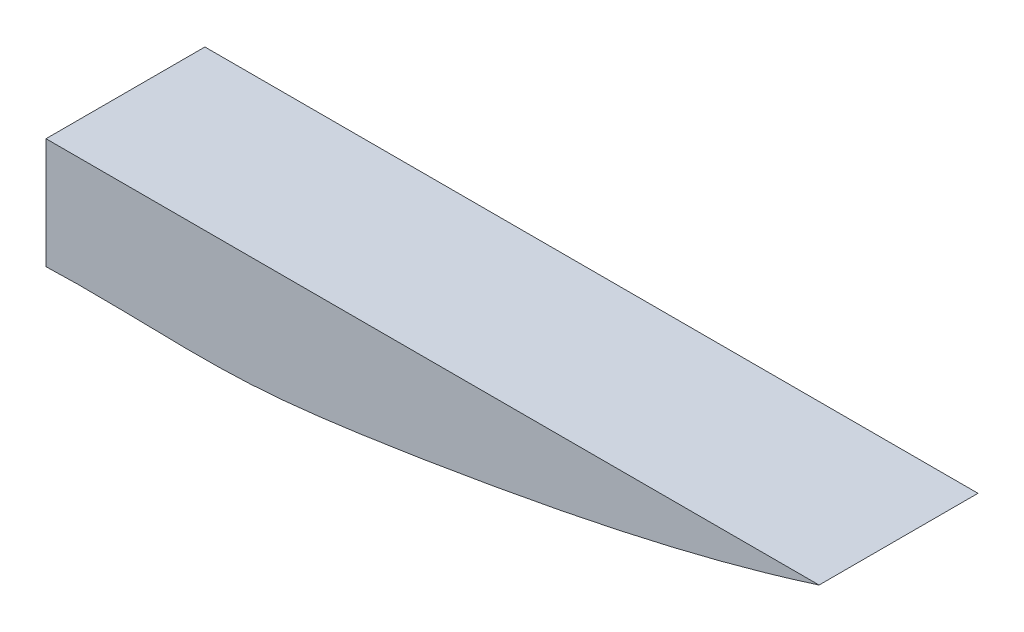
SolidWorks part; units mm, degrees
material "ABS PC"
ref_plane "Front Plane" through (0, 0, 0) normal (0, 0, 1) x (1, 0, 0)
ref_plane "Top Plane" through (0, 0, 0) normal (0, 1, 0) x (1, 0, 0)
ref_plane "Right Plane" through (0, 0, 0) normal (1, 0, 0) x (0, 0, -1)
sketch "Sketch1" plane through (0, 0, 0) normal (0, 0, 1) x (1, 0, 0)
  line L0 (0, 0) -> (0, -15)
  line L1 (0, 0) -> (104.6, 0)
  spline S0 degree 3 poles (0, -15) (8.7221, -14.6534) (23.1679, -15.8338) (42.3955, -13.4599) (68.6906, -9.2078) (89.2679, -4.9029) (104.6, 0) knots 0 0 0 0 0.246872 0.406938 0.546001 1 1 1 1
extrude "Boss-Extrude1" add sketch "Sketch1" against normal blind 21.5
